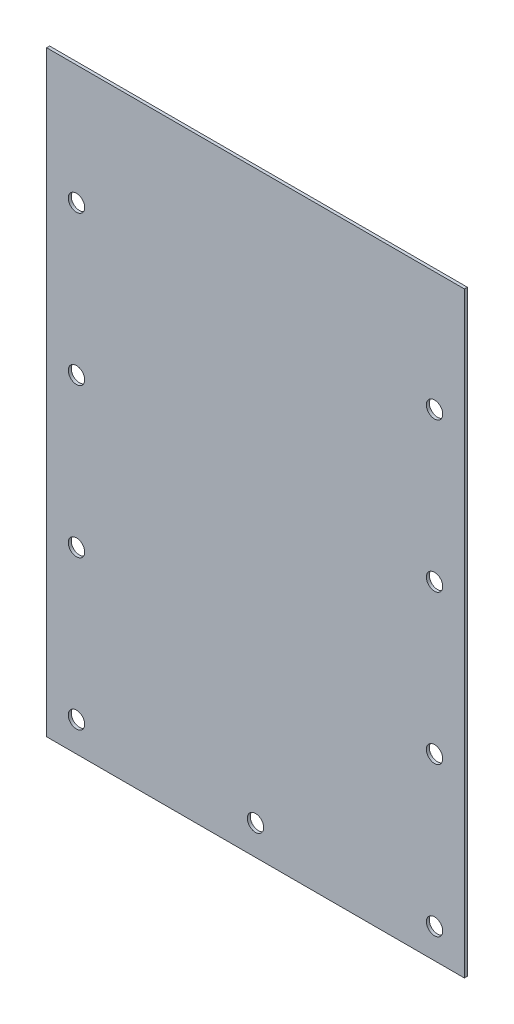
SolidWorks part; units mm, degrees
ref_plane "정면" through (0, 0, 0) normal (0, 0, 1) x (1, 0, 0)
ref_plane "윗면" through (0, 0, 0) normal (0, 1, 0) x (1, 0, 0)
ref_plane "우측면" through (0, 0, 0) normal (1, 0, 0) x (0, 0, -1)
sketch "스케치1" plane through (0, 0, 0) normal (0, 0, 1) x (1, 0, 0)
  line L1 (-70, -110) -> (70, -110)
  line L2 (-70, -110) -> (-70, 110)
  line L3 (-70, 110) -> (70, 110)
  line L4 (70, -110) -> (70, 110)
  line L5 (-70, -110) -> (70, 110) construction
  line L6 (-70, 110) -> (70, -110) construction
  line L7 (-60, -100) -> (60, -100) construction
  line L8 (-60, -100) -> (-60, 100) construction
  line L9 (-60, 100) -> (60, 100) construction
  line L10 (60, -100) -> (60, 100) construction
  line L11 (-60, -100) -> (60, 100) construction
  line L12 (-60, 100) -> (60, -100) construction
  point P0 (0, 0)
  point P6 (0, 0)
  point P12 (-60, 100)
  point P13 (60, 100)
  point P14 (60, -100)
  point P15 (-60, -100)
  point P16 (0, -100)
  point P17 (0, 0)
  point P19 (0, 0)
  point P20 (-60, -50)
  point P22 (0, 100)
  point P26 (-60, 0)
  point P27 (0, 100)
  point P29 (-60, 50)
  point P32 (60, -50)
  point P33 (60, 0)
  point P35 (60, 50)
  dimension "D1" = 140
  dimension "D2" = 220
  dimension "D3" = 10
  dimension "D4" = 10
  dimension "D5" = 50
  dimension "D6" = 50
extrude "보스-돌출1" add sketch "스케치1" along normal blind 1 contours L3 L4 L1 L2
hole_wizard "M5 여유 구멍1" positions "스케치2" profile "스케치3" hole size "M5" standard "KS" end condition through all
sketch "스케치2" plane through (0, 0, 0) normal (0, 0, -1) x (-1, 0, 0)
  point P0 (-60, 100)
  point P9 (0, 100)
  point P18 (60, 100)
  point P21 (60, 50)
  point P24 (60, -50)
  point P27 (60, 0)
  point P36 (60, -100)
  point P39 (-60, 50)
  point P42 (-60, -50)
  point P45 (-60, 0)
  point P54 (-60, -100)
  point P63 (0, -100)
sketch "스케치3" plane through (60, 100, 0) normal (1, 0, 0) x (0, 1, 0)
  line L0 (0, 0) -> (0, 1)
  line L1 (0, 1) -> (2.75, 1)
  line L2 (2.75, 1) -> (2.75, 0)
  line L5 (2.75, 0) -> (0, 0)
  line L11 (0, -6.35) -> (0, 107.95) construction
  dimension "관통 구멍 지름" = 5.5
  dimension "관통 구멍 깊이" = 1
sketch "스케치4" plane through (0, 0, 0) normal (0, 0, -1) x (-1, 0, 0)
  line L0 (70, -110) -> (70, 110) construction
  line L1 (-70, 110) -> (70, 110)
  line L2 (-70, 110) -> (-70, 90)
  line L3 (-70, 90) -> (70, 90)
  line L4 (70, 110) -> (70, 90)
  line L5 (-70, 110) -> (70, 90) construction
  line L6 (-70, 90) -> (70, 110) construction
  point P4 (0, 100)
  dimension "D1" = 20
extrude "컷-돌출1" cut sketch "스케치4" against normal blind 10
